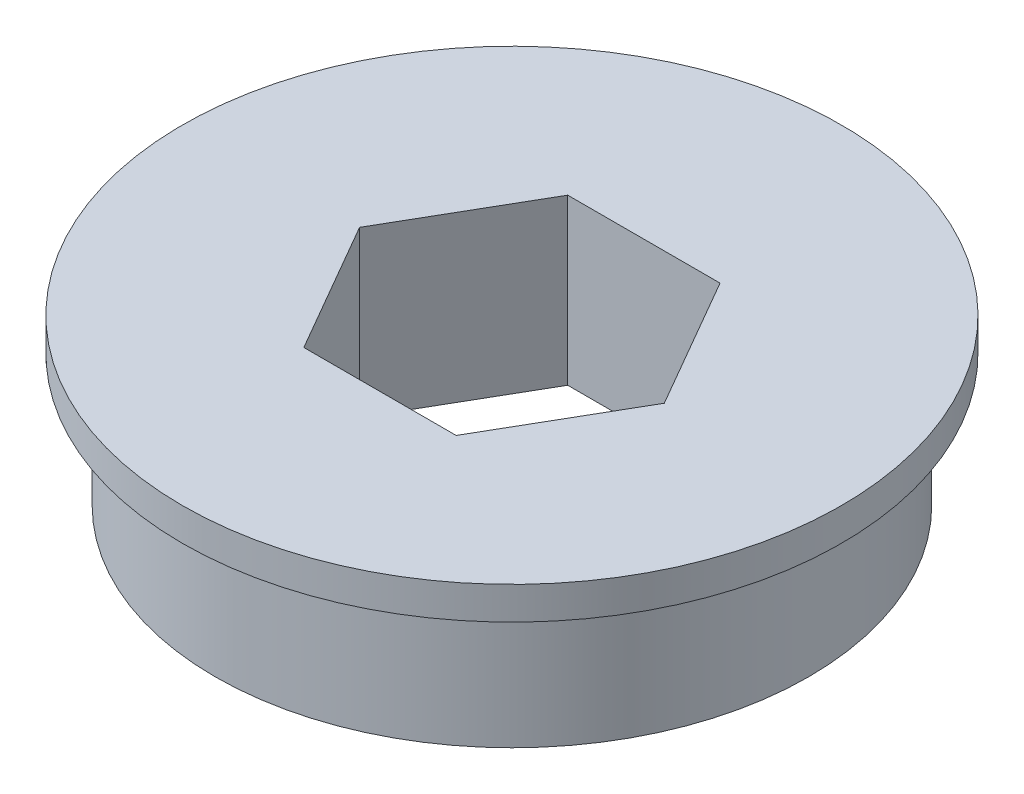
SolidWorks part; units mm, degrees
ref_plane "Front Plane" through (0, 0, 0) normal (0, 0, 1) x (1, 0, 0)
ref_plane "Top Plane" through (0, 0, 0) normal (0, 1, 0) x (1, 0, 0)
ref_plane "Right Plane" through (0, 0, 0) normal (1, 0, 0) x (0, 0, -1)
sketch "Sketch1" plane through (0, 0, 0) normal (0, 1, 0) x (1, 0, 0)
  line L1 (-3.6662, 6.35) -> (-7.3323, 0)
  line L2 (-7.3323, 0) -> (-3.6662, -6.35)
  line L3 (-3.6662, -6.35) -> (3.6662, -6.35)
  line L4 (3.6662, -6.35) -> (7.3323, 0)
  line L5 (7.3323, 0) -> (3.6662, 6.35)
  line L6 (3.6662, 6.35) -> (-3.6662, 6.35)
  circle A0 centre (0, 0) radius 14.2875
  circle A1 centre (0, 0) radius 6.35 construction
  dimension "D1" = 28.575
  dimension "D2" = 12.7
extrude "Boss-Extrude1" add sketch "Sketch1" along normal blind 7.9248
sketch "Sketch2" plane through (0, 7.9248, 0) normal (0, 1, 0) x (1, 0, 0)
  circle A0 centre (0, 0) radius 15.8623
  circle A1 centre (0, 0) radius 14.2875 construction
  circle A2 centre (0, 0) radius 14.2875
  dimension "D1" = 1.5748
extrude "Boss-Extrude2" add sketch "Sketch2" against normal blind 1.5748
